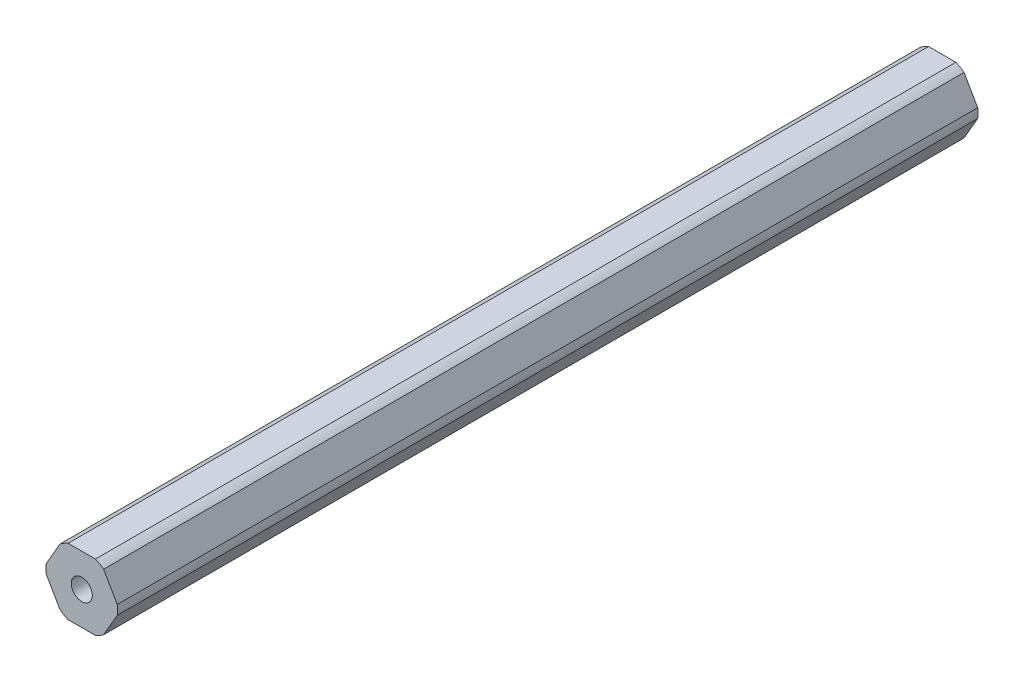
SolidWorks part; units mm, degrees
ref_plane "Front Plane" through (0, 0, 0) normal (0, 0, 1) x (1, 0, 0)
ref_plane "Top Plane" through (0, 0, 0) normal (0, 1, 0) x (1, 0, 0)
ref_plane "Right Plane" through (0, 0, 0) normal (1, 0, 0) x (0, 0, -1)
sketch "Sketch1" plane through (0, 0, 0) normal (0, 0, 1) x (1, 0, 0)
  line L1 (-4.1874, 5.4472) -> (-6.8111, 0.9028)
  line L2 (-6.8111, -0.9028) -> (-4.1874, -5.4472)
  line L3 (-2.6237, -6.35) -> (2.6237, -6.35)
  line L4 (4.1874, -5.4472) -> (6.8111, -0.9028)
  line L5 (6.8111, 0.9028) -> (4.1874, 5.4472)
  line L6 (2.6237, 6.35) -> (-2.6237, 6.35)
  circle A0 centre (0, 0) radius 6.35 construction
  arc A1 (-4.1874, -5.4472) -> (-2.6237, -6.35) centre (0, 0) ccw
  arc A2 (2.6237, -6.35) -> (4.1874, -5.4472) centre (0, 0) ccw
  arc A3 (6.8111, -0.9028) -> (2.6237, 6.35) centre (0, 0) ccw
  arc A4 (-2.6237, 6.35) -> (-4.1874, 5.4472) centre (0, 0) ccw
  arc A5 (-6.8111, 0.9028) -> (-6.8111, -0.9028) centre (0, 0) ccw
  circle A6 centre (0, 0) radius 2.0193
  point P11 (0, -6.35)
  dimension "D2" = 13.7414
  dimension "D3" = 4.0386
  dimension "D1" = 6.35
extrude "Boss-Extrude1" add sketch "Sketch1" along normal blind 165.1 contours L1 A5 L2 A1 L3 A2 L4 A3 L5 L6 A4 A6
